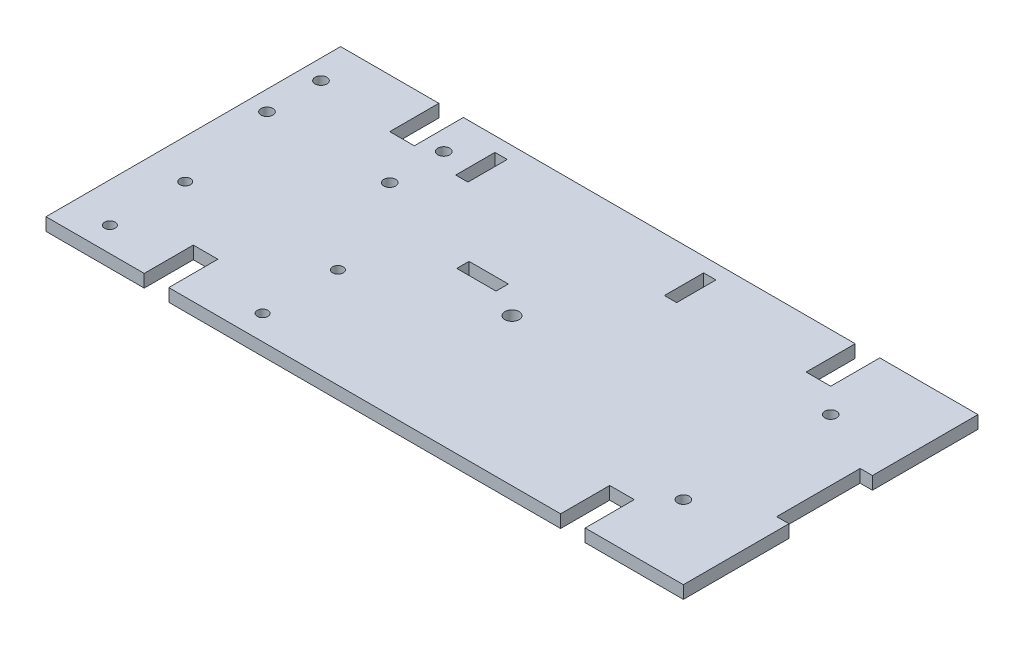
SolidWorks part; units mm, degrees
material "Cedar"
ref_plane "Front Plane" through (0, 0, 0) normal (0, 0, 1) x (1, 0, 0)
ref_plane "Top Plane" through (0, 0, 0) normal (0, 1, 0) x (1, 0, 0)
ref_plane "Right Plane" through (0, 0, 0) normal (1, 0, 0) x (0, 0, -1)
sketch "Sketch1" plane through (0, 0, 0) normal (0, 1, 0) x (1, 0, 0)
  line L0 (-164.846, 76.2) -> (-139.446, 76.2)
  line L9 (-139.446, 76.2) -> (-139.446, 63.5)
  line L10 (-139.446, 63.5) -> (-133.096, 63.5)
  line L11 (-133.096, 63.5) -> (-133.096, 76.2)
  line L12 (-133.096, 76.2) -> (-31.75, 76.2)
  line L13 (-31.75, 76.2) -> (-31.75, 63.5)
  line L14 (-31.75, 63.5) -> (-25.4, 63.5)
  line L15 (-25.4, 63.5) -> (-25.4, 76.2)
  line L16 (-25.4, 76.2) -> (0, 76.2)
  line L17 (0, 76.2) -> (0, 48.895)
  line L21 (0, 27.305) -> (0, 0)
  line L22 (0, 0) -> (-25.4, 0)
  line L23 (-25.4, 0) -> (-25.4, 12.7)
  line L24 (-25.4, 12.7) -> (-31.75, 12.7)
  line L25 (-31.75, 12.7) -> (-31.75, 0)
  line L26 (-31.75, 0) -> (-133.096, 0)
  line L27 (-133.096, 0) -> (-133.096, 12.7)
  line L28 (-133.096, 12.7) -> (-139.446, 12.7)
  line L29 (-139.446, 12.7) -> (-139.446, 0)
  line L30 (-139.446, 0) -> (-164.846, 0)
  line L31 (-164.846, 0) -> (-164.846, 27.305)
  line L33 (-164.846, 27.305) -> (-164.846, 48.895)
  line L35 (-164.846, 48.895) -> (-164.846, 76.2)
  line L36 (-82.423, 76.2) -> (-82.423, 0) construction
  line L37 (0, 48.895) -> (-3.175, 48.895)
  line L39 (0, 27.305) -> (-3.175, 27.305)
  line L40 (-3.175, 48.895) -> (-3.175, 27.305)
  line L41 (-164.846, 38.1) -> (-3.175, 38.1) construction
  circle A0 centre (-82.423, 38.1) radius 1.8288
  dimension "D8" = 3.6576
  dimension "D1" = 76.2
  dimension "D2" = 164.846
  dimension "D3" = 21.59
  dimension "D4" = 6.35
  dimension "D5" = 12.7
  dimension "D6" = 3.175
  dimension "D7" = 25.4
extrude "Boss-Extrude1" add sketch "Sketch1" along normal blind 3.302
sketch "Sketch2" plane through (0, 3.302, 0) normal (0, 1, 0) x (1, 0, 0)
  line L0 (-164.846, 76.2) -> (-164.846, 0) construction
  line L1 (-139.446, 76.2) -> (-164.846, 76.2) construction
  circle A0 centre (-159.766, 66.04) radius 1.524
  circle A1 centre (-128.016, 66.04) radius 1.524
  circle A2 centre (-128.016, 52.07) radius 1.524
  circle A3 centre (-159.766, 52.07) radius 1.524
  dimension "D2" = 13.97
  dimension "D3" = 3.048
  dimension "D1" = 31.75
  dimension "D4" = 5.08
  dimension "D5" = 10.16
extrude "Cut-Extrude1" cut sketch "Sketch2" against normal through all
sketch "Sketch3" plane through (0, 3.302, 0) normal (0, 1, 0) x (1, 0, 0)
  line L5 (-164.846, 76.2) -> (-164.846, 0) construction
  line L6 (-133.096, 0) -> (-31.75, 0) construction
  circle A0 centre (-154.686, 6.35) radius 1.375
  circle A1 centre (-115.186, 6.35) radius 1.375
  circle A2 centre (-115.186, 25.85) radius 1.375
  circle A3 centre (-154.686, 25.85) radius 1.375
  dimension "D3" = 2.75
  dimension "D1" = 10.16
  dimension "D2" = 6.35
  dimension "D4" = 19.5
  dimension "D5" = 39.5
extrude "Cut-Extrude2" cut sketch "Sketch3" against normal through all
sketch "Sketch4" plane through (0, 3.302, 0) normal (0, 1, 0) x (1, 0, 0)
  line L3 (-92.6188, 76.2) -> (-92.6188, 0) construction
  line L4 (-31.75, 76.2) -> (-133.096, 76.2) construction
  line L5 (-133.096, 0) -> (-31.75, 0) construction
  line L7 (-67.2188, 72.4668) -> (-67.2188, 62.3068)
  line L8 (-100.1419, 44.704) -> (-89.9819, 44.704)
  line L9 (-100.1419, 44.704) -> (-100.1419, 41.529)
  line L10 (-100.1419, 41.529) -> (-89.9819, 41.529)
  line L11 (-89.9819, 44.704) -> (-89.9819, 41.529)
  line L12 (-121.1938, 72.4668) -> (-118.0188, 72.4668)
  line L13 (-121.1938, 72.4668) -> (-121.1938, 62.3068)
  line L14 (-121.1938, 62.3068) -> (-118.0188, 62.3068)
  line L15 (-118.0188, 72.4668) -> (-118.0188, 62.3068)
  line L16 (-64.0438, 62.3068) -> (-67.2188, 62.3068)
  line L17 (-64.0438, 72.4668) -> (-64.0438, 62.3068)
  line L18 (-64.0438, 72.4668) -> (-67.2188, 72.4668)
  dimension "D1" = 10.16
  dimension "D2" = 3.175
  dimension "D3" = 31.496
  dimension "D4" = 50.8
extrude "Cut-Extrude3" cut sketch "Sketch4" against normal through all
sketch "Sketch5" plane through (0, 3.302, 0) normal (0, 1, 0) x (1, 0, 0)
  line L0 (-3.175, 38.1) -> (-164.846, 38.1) construction
  line L1 (-3.175, 27.305) -> (-3.175, 48.895) construction
  line L2 (-164.846, 76.2) -> (-164.846, 0) construction
  line L3 (0, 48.895) -> (0, 76.2) construction
  circle A0 centre (-19.05, 19.05) radius 1.524
  circle A1 centre (-19.05, 57.15) radius 1.524
  dimension "D1" = 3.048
  dimension "D2" = 38.1
  dimension "D3" = 19.05
extrude "Cut-Extrude4" cut sketch "Sketch5" against normal through all
